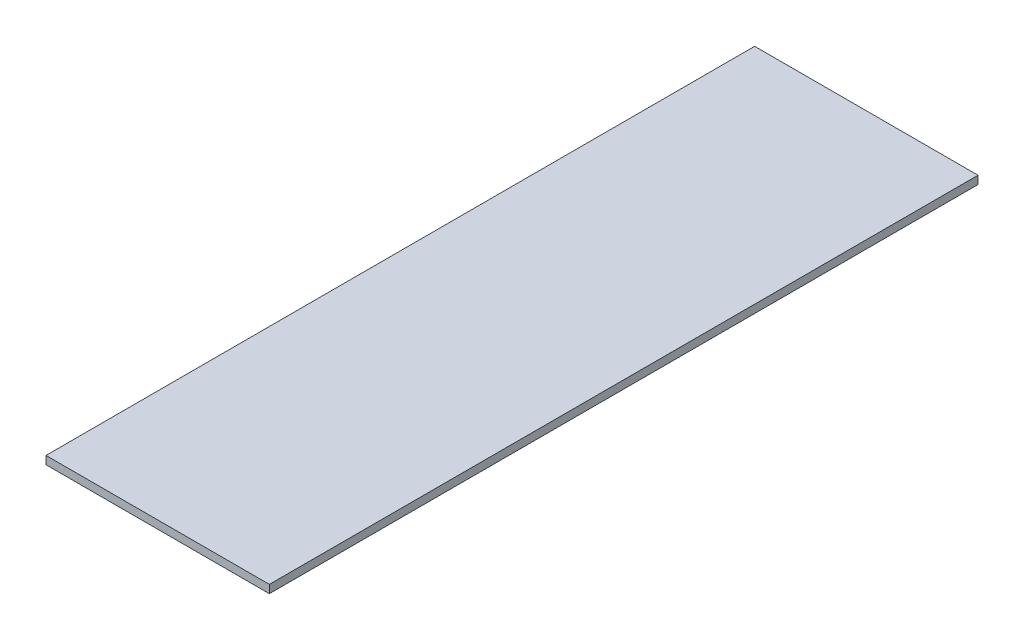
SolidWorks part; units mm, degrees
ref_plane "Спереди" through (0, 0, 0) normal (0, 0, 1) x (1, 0, 0)
ref_plane "Сверху" through (0, 0, 0) normal (0, 1, 0) x (1, 0, 0)
ref_plane "Справа" through (0, 0, 0) normal (1, 0, 0) x (0, 0, -1)
sketch "Эскиз1" plane through (0, 0, 0) normal (0, 1, 0) x (1, 0, 0)
  line L1 (249, -790) -> (-249, -790)
  line L2 (249, -790) -> (249, 790)
  line L3 (249, 790) -> (-249, 790)
  line L4 (-249, -790) -> (-249, 790)
  line L5 (249, -790) -> (-249, 790) construction
  line L6 (249, 790) -> (-249, -790) construction
  point P0 (0, 0)
  dimension "D1" = 1580
  dimension "D2" = 498
extrude "Бобышка-Вытянуть1" add sketch "Эскиз1" along normal blind 18
